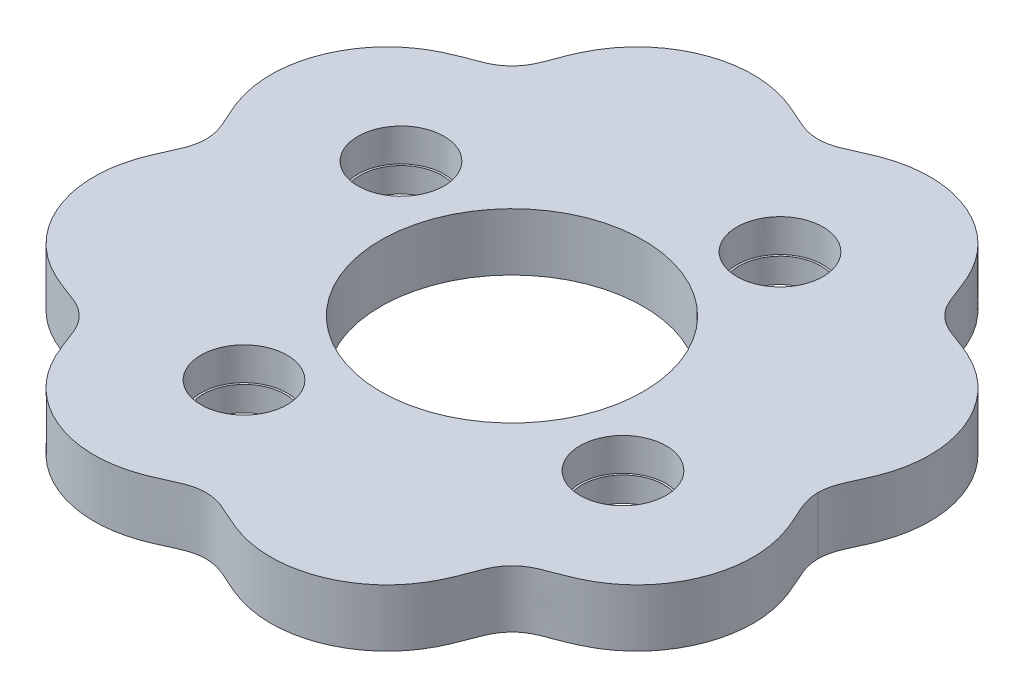
SolidWorks part; units mm, degrees
material "PET"
ref_plane "Front Plane" through (0, 0, 0) normal (0, 0, 1) x (1, 0, 0)
ref_plane "Top Plane" through (0, 0, 0) normal (0, 1, 0) x (1, 0, 0)
ref_plane "Right Plane" through (0, 0, 0) normal (1, 0, 0) x (0, 0, -1)
sketch "Sketch2" plane through (0, 0, 0) normal (0, 1, 0) x (1, 0, 0)
  line L0 (-37.5, 0) -> (37.5, 0) construction
  spline S0 degree 4 poles (36.9805, 20.0285) (37.2753, 19.6778) (37.8347, 18.9513) (38.4555, 17.9854) (39.0737, 16.7557) (39.5005, 15.6923) (39.7876, 14.8217) (40.0191, 13.9346) (40.1939, 13.0347) (40.3111, 12.1255) (40.3698, 11.2106) (40.3695, 10.2938) (40.3175, 9.4934) (40.2359, 8.8108) (40.1529, 8.3024) (40.0885, 7.9647) (40.0287, 7.6841) (39.9777, 7.4611) (39.9238, 7.2412) (39.8664, 7.0219) (39.8025, 6.7937) (39.7309, 6.5533) (39.6637, 6.3374) (39.6136, 6.1836) (39.5479, 5.991) (39.4755, 5.7851) (39.4027, 5.5855) (39.3311, 5.3965) (39.2407, 5.1663) (39.1279, 4.8896) (38.9903, 4.5651) (38.8283, 4.1989) (38.6621, 3.8341) (38.4352, 3.3438) (38.1502, 2.7272) (37.8212, 1.946) (37.5468, 0.9653) (37.4535, -0.0911) (37.5698, -1.0461) (37.7995, -1.8451) (38.0553, -2.5006) (38.2844, -3.0188) (38.5476, -3.5861) (38.8343, -4.2072) (39.213, -5.0714) (39.6429, -6.1955) (40.0348, -7.5456) (40.3091, -9.1291) (40.4025, -10.7334) (40.2923, -12.7392) (39.8007, -15.1154) (38.875, -17.3723) (37.5505, -19.4168) (36.2019, -20.9371) (34.9913, -22.0223) (33.6644, -22.9618) (32.4189, -23.6484) (31.3072, -24.1448) (30.4154, -24.4925) (29.7608, -24.7333) (29.1593, -24.9537) (28.6152, -25.1661) (27.9682, -25.4558) (27.2425, -25.8692) (26.4868, -26.4785) (25.7889, -27.3386) (25.3334, -28.1996) (25.0208, -28.9789) (24.7562, -29.6972) (24.5201, -30.3421) (24.1768, -31.23) (23.6857, -32.344) (23.006, -33.5933) (22.0744, -34.9257) (20.9963, -36.1426) (19.484, -37.5001) (17.4364, -38.8435) (15.1658, -39.787) (12.7656, -40.2907) (10.7279, -40.4037) (9.0981, -40.3067) (7.4903, -40.0231) (6.1205, -39.6185) (4.9809, -39.1759) (3.9811, -38.7332) (3.1077, -38.3232) (2.1628, -37.8962) (1.1027, -37.5687) (0, -37.4517) (-1.1027, -37.5687) (-2.1628, -37.8962) (-3.1077, -38.3232) (-3.9811, -38.7332) (-4.9809, -39.1759) (-6.1205, -39.6185) (-7.4903, -40.0231) (-9.0981, -40.3067) (-10.7279, -40.4037) (-12.7656, -40.2907) (-15.1658, -39.787) (-17.4364, -38.8435) (-19.484, -37.5001) (-20.9963, -36.1426) (-22.0744, -34.9257) (-23.006, -33.5933) (-23.6856, -32.3439) (-24.1768, -31.23) (-24.5707, -30.2109) (-24.8996, -29.3004) (-25.2674, -28.3245) (-25.7889, -27.3386) (-26.4868, -26.4785) (-27.2424, -25.8692) (-27.9682, -25.4558) (-28.6151, -25.166) (-29.1593, -24.9537) (-29.7608, -24.7333) (-30.4154, -24.4925) (-31.3072, -24.1448) (-32.4189, -23.6484) (-33.6644, -22.9618) (-34.9913, -22.0223) (-36.2019, -20.9371) (-37.5505, -19.4168) (-38.875, -17.3723) (-39.8007, -15.1154) (-40.2923, -12.7392) (-40.4025, -10.7334) (-40.3091, -9.1291) (-40.0348, -7.5456) (-39.6429, -6.1955) (-39.213, -5.0714) (-38.8343, -4.2072) (-38.5476, -3.5861) (-38.2844, -3.0188) (-38.0553, -2.5006) (-37.7995, -1.8451) (-37.5698, -1.0461) (-37.4535, -0.0911) (-37.5468, 0.9653) (-37.8212, 1.946) (-38.1502, 2.7272) (-38.4352, 3.3438) (-38.6621, 3.8341) (-38.8283, 4.1989) (-38.9903, 4.5651) (-39.1279, 4.8896) (-39.2407, 5.1663) (-39.3311, 5.3965) (-39.4027, 5.5855) (-39.4755, 5.7851) (-39.5479, 5.991) (-39.6136, 6.1836) (-39.6637, 6.3374) (-39.7309, 6.5533) (-39.8025, 6.7937) (-39.8664, 7.0219) (-39.9238, 7.2412) (-39.9777, 7.4611) (-40.0287, 7.6841) (-40.0885, 7.9647) (-40.1529, 8.3024) (-40.2359, 8.8108) (-40.3175, 9.4934) (-40.3695, 10.2938) (-40.3698, 11.2106) (-40.3111, 12.1255) (-40.1939, 13.0347) (-40.0191, 13.9346) (-39.7876, 14.8217) (-39.5005, 15.6923) (-39.0737, 16.7557) (-38.4555, 17.9854) (-37.8347, 18.9513) (-37.2753, 19.6778) (-36.9805, 20.0285) knots 0 0 0 0 0 0.010311 0.020621 0.025777 0.030932 0.036087 0.041243 0.046398 0.051553 0.056709 0.061864 0.067019 0.069597 0.072175 0.073463 0.074752 0.076041 0.07733 0.078618 0.079907 0.081196 0.082485 0.083613 0.084741 0.085869 0.086997 0.088125 0.089253 0.091509 0.093765 0.09602 0.098276 0.100532 0.105923 0.111314 0.117336 0.123359 0.129627 0.132815 0.136003 0.139191 0.142379 0.146891 0.151403 0.160427 0.169451 0.178475 0.1875 0.196524 0.214573 0.232831 0.24196 0.251089 0.260218 0.269348 0.278476 0.28304 0.287605 0.29089 0.294176 0.297462 0.300748 0.306838 0.312927 0.319161 0.325494 0.32866 0.331826 0.33639 0.340955 0.350083 0.359212 0.368341 0.37747 0.386599 0.404858 0.423193 0.432361 0.441528 0.450696 0.459863 0.46903 0.473614 0.478197 0.484473 0.490748 0.496943 0.503057 0.509252 0.515527 0.521803 0.526386 0.53097 0.540137 0.549304 0.558472 0.567639 0.576807 0.595142 0.613401 0.62253 0.631659 0.640788 0.649917 0.659045 0.66361 0.668174 0.674506 0.680839 0.687073 0.693162 0.699252 0.702538 0.705824 0.70911 0.712395 0.71696 0.721524 0.730652 0.739782 0.748911 0.75804 0.767169 0.785427 0.803476 0.8125 0.821525 0.830549 0.839573 0.848597 0.853109 0.857621 0.860809 0.863997 0.867185 0.870373 0.876641 0.882664 0.888686 0.894077 0.899468 0.901724 0.90398 0.906235 0.908491 0.910747 0.911875 0.913003 0.914131 0.915259 0.916387 0.917515 0.918804 0.920093 0.921382 0.92267 0.923959 0.925248 0.926537 0.927825 0.930403 0.932981 0.938136 0.943291 0.948447 0.953602 0.958757 0.963913 0.969068 0.974223 0.979379 0.989689 1 1 1 1 1 construction
  spline S1 degree 4 poles (37.5, 0) (37.5, -0.1537) (37.5167, -0.5857) (37.6013, -1.1559) (37.7995, -1.8451) (38.0553, -2.5006) (38.2844, -3.0188) (38.5476, -3.5861) (38.8343, -4.2072) (39.213, -5.0714) (39.6429, -6.1955) (40.0348, -7.5456) (40.3091, -9.1291) (40.4025, -10.7334) (40.2923, -12.7392) (39.8007, -15.1154) (38.875, -17.3723) (37.5505, -19.4168) (36.2019, -20.9371) (34.9913, -22.0223) (33.6644, -22.9618) (32.4189, -23.6484) (31.3072, -24.1448) (30.4154, -24.4925) (29.7608, -24.7333) (29.1593, -24.9537) (28.6152, -25.1661) (27.9682, -25.4558) (27.2425, -25.8692) (26.4868, -26.4785) (25.7889, -27.3386) (25.3334, -28.1996) (25.0208, -28.9789) (24.7562, -29.6972) (24.5201, -30.3421) (24.1768, -31.23) (23.6857, -32.344) (23.006, -33.5933) (22.0744, -34.9257) (20.9963, -36.1426) (19.484, -37.5001) (17.4364, -38.8435) (15.1658, -39.787) (12.7656, -40.2907) (10.7279, -40.4037) (9.0981, -40.3067) (7.4903, -40.0231) (6.1205, -39.6185) (4.9809, -39.1759) (3.9811, -38.7332) (3.1077, -38.3232) (2.1628, -37.8962) (1.1027, -37.5687) (0, -37.4517) (-1.1027, -37.5687) (-2.1628, -37.8962) (-3.1077, -38.3232) (-3.9811, -38.7332) (-4.9809, -39.1759) (-6.1205, -39.6185) (-7.4903, -40.0231) (-9.0981, -40.3067) (-10.7279, -40.4037) (-12.7656, -40.2907) (-15.1658, -39.787) (-17.4364, -38.8435) (-19.484, -37.5001) (-20.9963, -36.1426) (-22.0744, -34.9257) (-23.006, -33.5933) (-23.6856, -32.3439) (-24.1768, -31.23) (-24.5707, -30.2109) (-24.8996, -29.3004) (-25.2674, -28.3245) (-25.7889, -27.3386) (-26.4868, -26.4785) (-27.2424, -25.8692) (-27.9682, -25.4558) (-28.6151, -25.166) (-29.1593, -24.9537) (-29.7608, -24.7333) (-30.4154, -24.4925) (-31.3072, -24.1448) (-32.4189, -23.6484) (-33.6644, -22.9618) (-34.9913, -22.0223) (-36.2019, -20.9371) (-37.5505, -19.4168) (-38.875, -17.3723) (-39.8007, -15.1154) (-40.2923, -12.7392) (-40.4025, -10.7334) (-40.3091, -9.1291) (-40.0348, -7.5456) (-39.6429, -6.1955) (-39.213, -5.0714) (-38.8343, -4.2072) (-38.5476, -3.5861) (-38.2844, -3.0188) (-38.0553, -2.5006) (-37.7995, -1.8451) (-37.6013, -1.1559) (-37.5167, -0.5857) (-37.5, -0.1537) (-37.5, 0) knots 0.119901 0.119901 0.119901 0.119901 0.119901 0.123359 0.129627 0.132815 0.136003 0.139191 0.142379 0.146891 0.151403 0.160427 0.169451 0.178475 0.1875 0.196524 0.214573 0.232831 0.24196 0.251089 0.260218 0.269348 0.278476 0.28304 0.287605 0.29089 0.294176 0.297462 0.300748 0.306838 0.312927 0.319161 0.325494 0.32866 0.331826 0.33639 0.340955 0.350083 0.359212 0.368341 0.37747 0.386599 0.404858 0.423193 0.432361 0.441528 0.450696 0.459863 0.46903 0.473614 0.478197 0.484473 0.490748 0.496943 0.503057 0.509252 0.515527 0.521803 0.526386 0.53097 0.540137 0.549304 0.558472 0.567639 0.576807 0.595142 0.613401 0.62253 0.631659 0.640788 0.649917 0.659045 0.66361 0.668174 0.674506 0.680839 0.687073 0.693162 0.699252 0.702538 0.705824 0.70911 0.712395 0.71696 0.721524 0.730652 0.739782 0.748911 0.75804 0.767169 0.785427 0.803476 0.8125 0.821525 0.830549 0.839573 0.848597 0.853109 0.857621 0.860809 0.863997 0.867185 0.870373 0.876641 0.880099 0.880099 0.880099 0.880099 0.880099
  spline S2 degree 4 poles (37.5, 0) (37.5, 0.1537) (37.5167, 0.5857) (37.6013, 1.1559) (37.7995, 1.8451) (38.0553, 2.5006) (38.2844, 3.0188) (38.5476, 3.5861) (38.8343, 4.2072) (39.213, 5.0714) (39.6429, 6.1955) (40.0348, 7.5456) (40.3091, 9.1291) (40.4025, 10.7334) (40.2923, 12.7392) (39.8007, 15.1154) (38.875, 17.3723) (37.5505, 19.4168) (36.2019, 20.9371) (34.9913, 22.0223) (33.6644, 22.9618) (32.4189, 23.6484) (31.3072, 24.1448) (30.4154, 24.4925) (29.7608, 24.7333) (29.1593, 24.9537) (28.6152, 25.1661) (27.9682, 25.4558) (27.2425, 25.8692) (26.4868, 26.4785) (25.7889, 27.3386) (25.3334, 28.1996) (25.0208, 28.9789) (24.7562, 29.6972) (24.5201, 30.3421) (24.1768, 31.23) (23.6857, 32.344) (23.006, 33.5933) (22.0744, 34.9257) (20.9963, 36.1426) (19.484, 37.5001) (17.4364, 38.8435) (15.1658, 39.787) (12.7656, 40.2907) (10.7279, 40.4037) (9.0981, 40.3067) (7.4903, 40.0231) (6.1205, 39.6185) (4.9809, 39.1759) (3.9811, 38.7332) (3.1077, 38.3232) (2.1628, 37.8962) (1.1027, 37.5687) (0, 37.4517) (-1.1027, 37.5687) (-2.1628, 37.8962) (-3.1077, 38.3232) (-3.9811, 38.7332) (-4.9809, 39.1759) (-6.1205, 39.6185) (-7.4903, 40.0231) (-9.0981, 40.3067) (-10.7279, 40.4037) (-12.7656, 40.2907) (-15.1658, 39.787) (-17.4364, 38.8435) (-19.484, 37.5001) (-20.9963, 36.1426) (-22.0744, 34.9257) (-23.006, 33.5933) (-23.6856, 32.3439) (-24.1768, 31.23) (-24.5707, 30.2109) (-24.8996, 29.3004) (-25.2674, 28.3245) (-25.7889, 27.3386) (-26.4868, 26.4785) (-27.2424, 25.8692) (-27.9682, 25.4558) (-28.6151, 25.166) (-29.1593, 24.9537) (-29.7608, 24.7333) (-30.4154, 24.4925) (-31.3072, 24.1448) (-32.4189, 23.6484) (-33.6644, 22.9618) (-34.9913, 22.0223) (-36.2019, 20.9371) (-37.5505, 19.4168) (-38.875, 17.3723) (-39.8007, 15.1154) (-40.2923, 12.7392) (-40.4025, 10.7334) (-40.3091, 9.1291) (-40.0348, 7.5456) (-39.6429, 6.1955) (-39.213, 5.0714) (-38.8343, 4.2072) (-38.5476, 3.5861) (-38.2844, 3.0188) (-38.0553, 2.5006) (-37.7995, 1.8451) (-37.6013, 1.1559) (-37.5167, 0.5857) (-37.5, 0.1537) (-37.5, 0) knots 0.119901 0.119901 0.119901 0.119901 0.119901 0.123359 0.129627 0.132815 0.136003 0.139191 0.142379 0.146891 0.151403 0.160427 0.169451 0.178475 0.1875 0.196524 0.214573 0.232831 0.24196 0.251089 0.260218 0.269348 0.278476 0.28304 0.287605 0.29089 0.294176 0.297462 0.300748 0.306838 0.312927 0.319161 0.325494 0.32866 0.331826 0.33639 0.340955 0.350083 0.359212 0.368341 0.37747 0.386599 0.404858 0.423193 0.432361 0.441528 0.450696 0.459863 0.46903 0.473614 0.478197 0.484473 0.490748 0.496943 0.503057 0.509252 0.515527 0.521803 0.526386 0.53097 0.540137 0.549304 0.558472 0.567639 0.576807 0.595142 0.613401 0.62253 0.631659 0.640788 0.649917 0.659045 0.66361 0.668174 0.674506 0.680839 0.687073 0.693162 0.699252 0.702538 0.705824 0.70911 0.712395 0.71696 0.721524 0.730652 0.739782 0.748911 0.75804 0.767169 0.785427 0.803476 0.8125 0.821525 0.830549 0.839573 0.848597 0.853109 0.857621 0.860809 0.863997 0.867185 0.870373 0.876641 0.880099 0.880099 0.880099 0.880099 0.880099
extrude "Boss-Extrude1" add sketch "Sketch2" along normal blind 7 contours S2 S1
sketch "Sketch3" plane through (0, 7, 0) normal (0, 1, 0) x (1, 0, 0)
  line L0 (0, 0) -> (39.2649, -16.264) construction
  circle A0 centre (0, 0) radius 16
  circle A1 centre (23.097, -9.5671) radius 5.25
  circle A3 centre (-9.5671, -23.097) radius 5.25
  circle A4 centre (-23.097, 9.5671) radius 5.25
  circle A5 centre (9.5671, 23.097) radius 5.25
  spline S0 degree 4 poles (37.5, 0) (37.5, -0.1537) (37.5167, -0.5857) (37.6013, -1.1559) (37.7995, -1.8451) (38.0553, -2.5006) (38.2844, -3.0188) (38.5476, -3.5861) (38.8343, -4.2072) (39.213, -5.0714) (39.6429, -6.1955) (40.0348, -7.5456) (40.3091, -9.1291) (40.4025, -10.7334) (40.2923, -12.7392) (39.8007, -15.1154) (38.875, -17.3723) (37.5505, -19.4168) (36.2019, -20.9371) (34.9913, -22.0223) (33.6644, -22.9618) (32.4189, -23.6484) (31.3072, -24.1448) (30.4154, -24.4925) (29.7608, -24.7333) (29.1593, -24.9537) (28.6152, -25.1661) (27.9682, -25.4558) (27.2425, -25.8692) (26.4868, -26.4785) (25.7889, -27.3386) (25.3334, -28.1996) (25.0208, -28.9789) (24.7562, -29.6972) (24.5201, -30.3421) (24.1768, -31.23) (23.6857, -32.344) (23.006, -33.5933) (22.0744, -34.9257) (20.9963, -36.1426) (19.484, -37.5001) (17.4364, -38.8435) (15.1658, -39.787) (12.7656, -40.2907) (10.7279, -40.4037) (9.0981, -40.3067) (7.4903, -40.0231) (6.1205, -39.6185) (4.9809, -39.1759) (3.9811, -38.7332) (3.1077, -38.3232) (2.1628, -37.8962) (1.1027, -37.5687) (0, -37.4517) (-1.1027, -37.5687) (-2.1628, -37.8962) (-3.1077, -38.3232) (-3.9811, -38.7332) (-4.9809, -39.1759) (-6.1205, -39.6185) (-7.4903, -40.0231) (-9.0981, -40.3067) (-10.7279, -40.4037) (-12.7656, -40.2907) (-15.1658, -39.787) (-17.4364, -38.8435) (-19.484, -37.5001) (-20.9963, -36.1426) (-22.0744, -34.9257) (-23.006, -33.5933) (-23.6856, -32.3439) (-24.1768, -31.23) (-24.5707, -30.2109) (-24.8996, -29.3004) (-25.2674, -28.3245) (-25.7889, -27.3386) (-26.4868, -26.4785) (-27.2424, -25.8692) (-27.9682, -25.4558) (-28.6151, -25.166) (-29.1593, -24.9537) (-29.7608, -24.7333) (-30.4154, -24.4925) (-31.3072, -24.1448) (-32.4189, -23.6484) (-33.6644, -22.9618) (-34.9913, -22.0223) (-36.2019, -20.9371) (-37.5505, -19.4168) (-38.875, -17.3723) (-39.8007, -15.1154) (-40.2923, -12.7392) (-40.4025, -10.7334) (-40.3091, -9.1291) (-40.0348, -7.5456) (-39.6429, -6.1955) (-39.213, -5.0714) (-38.8343, -4.2072) (-38.5476, -3.5861) (-38.2844, -3.0188) (-38.0553, -2.5006) (-37.7995, -1.8451) (-37.6013, -1.1559) (-37.5167, -0.5857) (-37.5, -0.1537) (-37.5, 0) knots 0.119901 0.119901 0.119901 0.119901 0.119901 0.123359 0.129627 0.132815 0.136003 0.139191 0.142379 0.146891 0.151403 0.160427 0.169451 0.178475 0.1875 0.196524 0.214573 0.232831 0.24196 0.251089 0.260218 0.269348 0.278476 0.28304 0.287605 0.29089 0.294176 0.297462 0.300748 0.306838 0.312927 0.319161 0.325494 0.32866 0.331826 0.33639 0.340955 0.350083 0.359212 0.368341 0.37747 0.386599 0.404858 0.423193 0.432361 0.441528 0.450696 0.459863 0.46903 0.473614 0.478197 0.484473 0.490748 0.496943 0.503057 0.509252 0.515527 0.521803 0.526386 0.53097 0.540137 0.549304 0.558472 0.567639 0.576807 0.595142 0.613401 0.62253 0.631659 0.640788 0.649917 0.659045 0.66361 0.668174 0.674506 0.680839 0.687073 0.693162 0.699252 0.702538 0.705824 0.70911 0.712395 0.71696 0.721524 0.730652 0.739782 0.748911 0.75804 0.767169 0.785427 0.803476 0.8125 0.821525 0.830549 0.839573 0.848597 0.853109 0.857621 0.860809 0.863997 0.867185 0.870373 0.876641 0.880099 0.880099 0.880099 0.880099 0.880099 construction
  point P18 (0, 0)
  dimension "D1" = 32
  dimension "D2" = 10.5
  dimension "D4" = 25
  dimension "D5" = 4
extrude "Cut-Extrude1" cut sketch "Sketch3" against normal blind 7
sketch "Sketch4" plane through (0, 0, 0) normal (0, -1, 0) x (1, 0, 0)
  spline S4 degree 3 poles (-3922.8422, 946.158) (-178.574, 87.803) (-28.4361, 25.2826) (-37.8533, -2.585) (-38.1471, -3.1952) (-38.7107, -4.4187) (-38.9828, -5.0336) (-39.4508, -6.2882) (-39.648, -6.9276) (-39.8757, -7.9088) (-39.9403, -8.2396) (-40.0461, -8.9088) (-40.0873, -9.2487) (-40.1729, -10.2702) (-40.1796, -10.9476) (-40.0964, -12.2955) (-40.0066, -12.966) (-39.7983, -13.9664) (-39.7162, -14.2999) (-39.5299, -14.9551) (-39.4254, -15.2779) (-39.079, -16.2318) (-38.8042, -16.8488) (-38.1662, -18.0446) (-37.7995, -18.6276) (-36.9951, -19.7223) (-36.557, -20.2365) (-35.6094, -21.1989) (-35.0988, -21.6477) (-34.0068, -22.4733) (-33.4366, -22.8413) (-32.2526, -23.4966) (-31.6381, -23.7828) (-30.6936, -24.1698) (-30.3749, -24.292) (-29.7353, -24.5302) (-29.4141, -24.6459) (-28.7761, -24.8878) (-28.4596, -25.0146) (-27.8419, -25.305) (-27.5385, -25.4704) (-26.9685, -25.8482) (-26.7027, -26.0593) (-26.2122, -26.5296) (-25.9857, -26.7918) (-25.5865, -27.3477) (-25.4133, -27.6409) (-25.1061, -28.2501) (-24.9721, -28.5662) (-24.722, -29.2071) (-24.6047, -29.5314) (-24.366, -30.178) (-24.2449, -30.5004) (-23.862, -31.4579) (-23.58, -32.0828) (-22.9307, -33.2897) (-22.5646, -33.8723) (-21.9447, -34.7109) (-21.7254, -34.9856) (-21.2703, -35.5135) (-21.0341, -35.7676) (-20.2998, -36.5011) (-19.7765, -36.9518) (-18.6627, -37.777) (-18.0672, -38.1536) (-16.8421, -38.8083) (-16.2104, -39.0887) (-15.2346, -39.4401) (-14.9046, -39.5456) (-14.235, -39.7331) (-13.894, -39.8152) (-12.1831, -40.161) (-10.8043, -40.2342) (-9.068, -40.0667) (-8.72, -40.0198) (-8.034, -39.9014) (-7.6946, -39.8297) (-6.6868, -39.5791) (-6.0289, -39.3634) (-4.7349, -38.8569) (-4.0997, -38.5639) (-2.8312, -37.9786) (-2.1955, -37.6898) (-1.1773, -37.4157) (-0.8309, -37.3518) (-0.1388, -37.2909) (0.2091, -37.2929) (0.9087, -37.3638) (1.2541, -37.4328) (1.9235, -37.621) (2.2502, -37.7405) (2.8946, -38.0077) (3.2126, -38.1544) (3.8487, -38.4482) (4.1667, -38.5954) (5.126, -39.018) (5.773, -39.274) (7.0935, -39.6938) (7.7666, -39.859) (8.7979, -40.0311) (9.1453, -40.076) (9.8476, -40.1396) (10.2044, -40.1583) (11.9811, -40.1834) (13.3741, -39.9912) (15.0807, -39.4906) (15.419, -39.3775) (16.0811, -39.1284) (16.4062, -38.9921) (17.364, -38.5485) (17.9792, -38.2067) (18.8662, -37.6232) (19.1571, -37.416) (19.72, -36.9818) (19.9916, -36.7554) (20.7778, -36.0486) (21.2637, -35.5408) (21.9348, -34.7238) (22.1489, -34.4422) (22.5573, -33.8603) (22.7513, -33.5603) (23.2966, -32.6452) (23.6131, -32.0104) (24.035, -31.0305) (24.1671, -30.6994) (24.4207, -30.0336) (24.5422, -29.6985) (24.7899, -29.0303) (24.9163, -28.6973) (25.203, -28.0449) (25.3653, -27.7235) (25.7389, -27.1186) (25.9496, -26.8348) (26.4253, -26.3096) (26.6934, -26.0663) (27.2624, -25.6405) (27.5646, -25.4559) (28.1962, -25.1299) (28.5258, -24.9886) (29.1951, -24.726) (29.5346, -24.6036) (30.211, -24.3537) (30.5481, -24.2267) (31.5472, -23.8241) (32.1968, -23.526) (33.4451, -22.8381) (34.0446, -22.4496) (34.9029, -21.793) (35.1822, -21.5619) (35.7264, -21.0739) (35.9929, -20.8154) (36.7549, -20.0151) (37.2156, -19.4476) (38.0459, -18.2477) (38.4158, -17.6149) (39.0608, -16.2832) (39.3278, -15.6011) (39.7553, -14.2058) (39.9157, -13.4925) (40.0733, -12.3983) (40.1117, -12.0294) (40.1591, -11.2964) (40.1684, -10.9307) (40.1534, -9.836) (40.0865, -9.1093) (39.8999, -8.0241) (39.8229, -7.6619) (39.642, -6.9461) (39.5382, -6.593) (39.1911, -5.5467) (38.9098, -4.8672) (38.4549, -3.8599) (38.2979, -3.5261) (37.9924, -2.8554) (37.8446, -2.5182) (37.5906, -1.8289) (37.4849, -1.4765) (32.1786, 25.0386) (201.3355, 100.2032) (2476.1492, -3163.1826) knots -0.660189 -0.660189 -0.660189 -0.660189 0.015625 0.015625 0.03125 0.03125 0.046875 0.046875 0.0625 0.0625 0.070312 0.070312 0.078125 0.078125 0.09375 0.09375 0.109375 0.109375 0.117187 0.117187 0.125 0.125 0.140625 0.140625 0.15625 0.15625 0.171875 0.171875 0.1875 0.1875 0.203125 0.203125 0.21875 0.21875 0.226562 0.226562 0.234375 0.234375 0.242187 0.242187 0.25 0.25 0.257812 0.257812 0.265625 0.265625 0.273437 0.273437 0.28125 0.28125 0.289062 0.289062 0.296875 0.296875 0.3125 0.3125 0.328125 0.328125 0.335937 0.335937 0.34375 0.34375 0.359375 0.359375 0.375 0.375 0.390625 0.390625 0.398437 0.398437 0.40625 0.40625 0.4375 0.4375 0.445312 0.445312 0.453125 0.453125 0.46875 0.46875 0.484375 0.484375 0.5 0.5 0.507812 0.507812 0.515625 0.515625 0.523437 0.523437 0.53125 0.53125 0.539062 0.539062 0.546875 0.546875 0.5625 0.5625 0.578125 0.578125 0.585937 0.585937 0.59375 0.59375 0.625 0.625 0.632812 0.632812 0.640625 0.640625 0.65625 0.65625 0.664062 0.664062 0.671875 0.671875 0.6875 0.6875 0.695312 0.695312 0.703125 0.703125 0.71875 0.71875 0.726562 0.726562 0.734375 0.734375 0.742187 0.742187 0.75 0.75 0.757812 0.757812 0.765625 0.765625 0.773437 0.773437 0.78125 0.78125 0.789062 0.789062 0.796875 0.796875 0.8125 0.8125 0.828125 0.828125 0.835937 0.835937 0.84375 0.84375 0.859375 0.859375 0.875 0.875 0.890625 0.890625 0.90625 0.90625 0.914062 0.914062 0.921875 0.921875 0.9375 0.9375 0.945312 0.945312 0.953125 0.953125 0.96875 0.96875 0.976562 0.976562 0.984375 0.984375 0.992187 0.992187 1.553035 1.553035 1.553035 1.553035 only from (-37.3, 0) to (37.3, 0)
  spline S5 degree 3 poles (3937.7854, -882.9619) (188.4371, -88.2123) (28.4038, -25.8804) (37.8317, 2.5321) (38.1169, 3.1309) (38.67, 4.3291) (38.9391, 4.9306) (39.406, 6.1564) (39.605, 6.7803) (39.9166, 8.056) (40.0298, 8.7075) (40.1293, 9.7073) (40.1505, 10.0435) (40.1686, 10.7108) (40.1657, 11.0433) (40.1219, 12.0378) (40.046, 12.6965) (39.8009, 14.0056) (39.6299, 14.66) (39.2033, 15.9228) (38.9476, 16.535) (38.3524, 17.7213) (38.0116, 18.2974) (36.8656, 19.953) (35.9651, 20.9257) (34.6682, 21.9774) (34.3991, 22.18) (33.8491, 22.5642) (33.5682, 22.7458) (32.7084, 23.2605) (32.1122, 23.5629) (30.8834, 24.1035) (30.2535, 24.3387) (28.9923, 24.8027) (28.3593, 25.0337) (27.173, 25.6725) (26.6404, 26.0718) (25.7322, 27.0751) (25.3881, 27.6463) (24.9705, 28.5655) (24.8471, 28.881) (24.6087, 29.5163) (24.4932, 29.836) (24.1362, 30.7892) (23.8828, 31.4162) (23.0112, 33.2354) (22.2825, 34.3665) (21.1418, 35.6532) (20.9009, 35.9055) (20.4029, 36.3896) (20.1462, 36.621) (19.3542, 37.2845) (18.7968, 37.6859) (17.9172, 38.2274) (17.6167, 38.3978) (17.0008, 38.7178) (16.6853, 38.8674) (15.7319, 39.2776) (15.0821, 39.5029) (13.7545, 39.8588) (13.0763, 39.9895) (11.6925, 40.1507) (11.0033, 40.1794) (9.6304, 40.1362) (8.9466, 40.0641) (7.9251, 39.8793) (7.5841, 39.8046) (6.9111, 39.6316) (6.5788, 39.5334) (5.5932, 39.2068) (4.9518, 38.945) (4.0012, 38.5197) (3.6862, 38.3727) (3.0549, 38.0823) (2.7387, 37.939) (1.7744, 37.5551) (1.1084, 37.3657) (-0.3132, 37.2631) (-1.0098, 37.3537) (-2.3731, 37.7595) (-3.0204, 38.0657) (-4.3192, 38.6656) (-4.971, 38.9584) (-6.3033, 39.4574) (-6.9832, 39.6657) (-8.0287, 39.9006) (-8.3815, 39.9661) (-9.096, 40.0703) (-9.4592, 40.109) (-10.5423, 40.1818) (-11.2606, 40.1739) (-12.6902, 40.0495) (-13.4023, 39.9326) (-14.8151, 39.5876) (-15.4996, 39.3636) (-16.8266, 38.8168) (-17.469, 38.4941) (-18.4002, 37.9335) (-18.7053, 37.7335) (-19.294, 37.3147) (-19.5789, 37.095) (-20.4061, 36.4056) (-20.9207, 35.9057) (-21.636, 35.094) (-21.8657, 34.8121) (-22.3022, 34.2315) (-22.5079, 33.9343) (-23.0891, 33.0233) (-23.428, 32.3894) (-24.0267, 31.0784) (-24.2847, 30.4) (-24.7858, 29.0385) (-25.0297, 28.3549) (-25.5555, 27.397) (-25.7572, 27.0906) (-26.2108, 26.5294) (-26.4639, 26.2717) (-27.0247, 25.8042) (-27.3276, 25.5991) (-27.9582, 25.243) (-28.288, 25.0905) (-28.9629, 24.8128) (-29.3068, 24.687) (-29.9941, 24.4342) (-30.3374, 24.3073) (-31.3574, 23.9062) (-32.0234, 23.6106) (-33.3074, 22.9225) (-33.9261, 22.5314) (-34.8143, 21.8642) (-35.1027, 21.6291) (-35.6549, 21.1411) (-35.9202, 20.8872) (-36.6842, 20.0966) (-37.1512, 19.5312) (-37.7877, 18.6247) (-37.9897, 18.3116) (-38.3661, 17.6752) (-38.5409, 17.3513) (-39.0264, 16.3632) (-39.2984, 15.6825) (-39.7376, 14.2767) (-39.9046, 13.5479) (-40.12, 12.094) (-40.1708, 11.3634) (-40.1608, 10.2619) (-40.143, 9.8938) (-40.0776, 9.1558) (-40.03, 8.7868) (-39.8455, 7.6961) (-39.6659, 6.9845) (-39.2071, 5.5888) (-38.9258, 4.9045) (-38.4691, 3.8906) (-38.3112, 3.5547) (-38.0034, 2.8801) (-37.8539, 2.541) (-37.5965, 1.8472) (-37.4888, 1.4922) (-32.3669, -23.8258) (-185.1413, -99.6898) (-2326.352, 3274.32) knots -0.686781 -0.686781 -0.686781 -0.686781 0.015625 0.015625 0.03125 0.03125 0.046875 0.046875 0.0625 0.0625 0.078125 0.078125 0.085938 0.085938 0.09375 0.09375 0.109375 0.109375 0.125 0.125 0.140625 0.140625 0.15625 0.15625 0.1875 0.1875 0.195313 0.195313 0.203125 0.203125 0.21875 0.21875 0.234375 0.234375 0.25 0.25 0.265625 0.265625 0.28125 0.28125 0.289063 0.289063 0.296875 0.296875 0.3125 0.3125 0.34375 0.34375 0.351563 0.351563 0.359375 0.359375 0.375 0.375 0.382813 0.382813 0.390625 0.390625 0.40625 0.40625 0.421875 0.421875 0.4375 0.4375 0.453125 0.453125 0.460938 0.460938 0.46875 0.46875 0.484375 0.484375 0.492188 0.492188 0.5 0.5 0.515625 0.515625 0.53125 0.53125 0.546875 0.546875 0.5625 0.5625 0.578125 0.578125 0.585938 0.585938 0.59375 0.59375 0.609375 0.609375 0.625 0.625 0.640625 0.640625 0.65625 0.65625 0.664063 0.664063 0.671875 0.671875 0.6875 0.6875 0.695313 0.695313 0.703125 0.703125 0.71875 0.71875 0.734375 0.734375 0.75 0.75 0.757813 0.757813 0.765625 0.765625 0.773438 0.773438 0.78125 0.78125 0.789063 0.789063 0.796875 0.796875 0.8125 0.8125 0.828125 0.828125 0.835938 0.835938 0.84375 0.84375 0.859375 0.859375 0.867188 0.867188 0.875 0.875 0.890625 0.890625 0.90625 0.90625 0.921875 0.921875 0.929688 0.929688 0.9375 0.9375 0.953125 0.953125 0.96875 0.96875 0.976563 0.976563 0.984375 0.984375 0.992188 0.992188 1.522491 1.522491 1.522491 1.522491 only from (37.3, 0) to (-37.3, 0)
  spline S6 degree 3 poles (-37.3, 0) (-37.3, -0.6769) (-37.4276, -1.3255) (-37.8533, -2.585) (-38.1471, -3.1952) (-38.7107, -4.4187) (-38.9828, -5.0336) (-39.4508, -6.2882) (-39.648, -6.9276) (-39.8757, -7.9088) (-39.9403, -8.2396) (-40.0461, -8.9088) (-40.0873, -9.2487) (-40.1729, -10.2702) (-40.1796, -10.9476) (-40.0964, -12.2955) (-40.0066, -12.966) (-39.7983, -13.9664) (-39.7162, -14.2999) (-39.5299, -14.9551) (-39.4254, -15.2779) (-39.079, -16.2318) (-38.8042, -16.8488) (-38.1662, -18.0446) (-37.7995, -18.6276) (-36.9951, -19.7223) (-36.557, -20.2365) (-35.6094, -21.1989) (-35.0988, -21.6477) (-34.0068, -22.4733) (-33.4366, -22.8413) (-32.2526, -23.4966) (-31.6381, -23.7828) (-30.6936, -24.1698) (-30.3749, -24.292) (-29.7353, -24.5302) (-29.4141, -24.6459) (-28.7761, -24.8878) (-28.4596, -25.0146) (-27.8419, -25.305) (-27.5385, -25.4704) (-26.9685, -25.8482) (-26.7027, -26.0593) (-26.2122, -26.5296) (-25.9857, -26.7918) (-25.5865, -27.3477) (-25.4133, -27.6409) (-25.1061, -28.2501) (-24.9721, -28.5662) (-24.722, -29.2071) (-24.6047, -29.5314) (-24.366, -30.178) (-24.2449, -30.5004) (-23.862, -31.4579) (-23.58, -32.0828) (-22.9307, -33.2897) (-22.5646, -33.8723) (-21.9447, -34.7109) (-21.7254, -34.9856) (-21.2703, -35.5135) (-21.0341, -35.7676) (-20.2998, -36.5011) (-19.7765, -36.9518) (-18.6627, -37.777) (-18.0672, -38.1536) (-16.8421, -38.8083) (-16.2104, -39.0887) (-15.2346, -39.4401) (-14.9046, -39.5456) (-14.235, -39.7331) (-13.894, -39.8152) (-12.1831, -40.161) (-10.8043, -40.2342) (-9.068, -40.0667) (-8.72, -40.0198) (-8.034, -39.9014) (-7.6946, -39.8297) (-6.6868, -39.5791) (-6.0289, -39.3634) (-4.7349, -38.8569) (-4.0997, -38.5639) (-2.8312, -37.9786) (-2.1955, -37.6898) (-1.1773, -37.4157) (-0.8309, -37.3518) (-0.1388, -37.2909) (0.2091, -37.2929) (0.9087, -37.3638) (1.2541, -37.4328) (1.9235, -37.621) (2.2502, -37.7405) (2.8946, -38.0077) (3.2126, -38.1544) (3.8487, -38.4482) (4.1667, -38.5954) (5.126, -39.018) (5.773, -39.274) (7.0935, -39.6938) (7.7666, -39.859) (8.7979, -40.0311) (9.1453, -40.076) (9.8476, -40.1396) (10.2044, -40.1583) (11.9811, -40.1834) (13.3741, -39.9912) (15.0807, -39.4906) (15.419, -39.3775) (16.0811, -39.1284) (16.4062, -38.9921) (17.364, -38.5485) (17.9792, -38.2067) (18.8662, -37.6232) (19.1571, -37.416) (19.72, -36.9818) (19.9916, -36.7554) (20.7778, -36.0486) (21.2637, -35.5408) (21.9348, -34.7238) (22.1489, -34.4422) (22.5573, -33.8603) (22.7513, -33.5603) (23.2966, -32.6452) (23.6131, -32.0104) (24.035, -31.0305) (24.1671, -30.6994) (24.4207, -30.0336) (24.5422, -29.6985) (24.7899, -29.0303) (24.9163, -28.6973) (25.203, -28.0449) (25.3653, -27.7235) (25.7389, -27.1186) (25.9496, -26.8348) (26.4253, -26.3096) (26.6934, -26.0663) (27.2624, -25.6405) (27.5646, -25.4559) (28.1962, -25.1299) (28.5258, -24.9886) (29.1951, -24.726) (29.5346, -24.6036) (30.211, -24.3537) (30.5481, -24.2267) (31.5472, -23.8241) (32.1968, -23.526) (33.4451, -22.8381) (34.0446, -22.4496) (34.9029, -21.793) (35.1822, -21.5619) (35.7264, -21.0739) (35.9929, -20.8154) (36.7549, -20.0151) (37.2156, -19.4476) (38.0459, -18.2477) (38.4158, -17.6149) (39.0608, -16.2832) (39.3278, -15.6011) (39.7553, -14.2058) (39.9157, -13.4925) (40.0733, -12.3983) (40.1117, -12.0294) (40.1591, -11.2964) (40.1684, -10.9307) (40.1534, -9.836) (40.0865, -9.1093) (39.8999, -8.0241) (39.8229, -7.6619) (39.642, -6.9461) (39.5382, -6.593) (39.1911, -5.5467) (38.9098, -4.8672) (38.4549, -3.8599) (38.2979, -3.5261) (37.9924, -2.8554) (37.8446, -2.5182) (37.5906, -1.8289) (37.4849, -1.4765) (37.3391, -0.7479) (37.3, -0.3741) (37.3, 0) knots 0 0 0 0 0.015625 0.015625 0.03125 0.03125 0.046875 0.046875 0.0625 0.0625 0.070312 0.070312 0.078125 0.078125 0.09375 0.09375 0.109375 0.109375 0.117187 0.117187 0.125 0.125 0.140625 0.140625 0.15625 0.15625 0.171875 0.171875 0.1875 0.1875 0.203125 0.203125 0.21875 0.21875 0.226562 0.226562 0.234375 0.234375 0.242187 0.242187 0.25 0.25 0.257812 0.257812 0.265625 0.265625 0.273437 0.273437 0.28125 0.28125 0.289062 0.289062 0.296875 0.296875 0.3125 0.3125 0.328125 0.328125 0.335937 0.335937 0.34375 0.34375 0.359375 0.359375 0.375 0.375 0.390625 0.390625 0.398437 0.398437 0.40625 0.40625 0.4375 0.4375 0.445312 0.445312 0.453125 0.453125 0.46875 0.46875 0.484375 0.484375 0.5 0.5 0.507812 0.507812 0.515625 0.515625 0.523437 0.523437 0.53125 0.53125 0.539062 0.539062 0.546875 0.546875 0.5625 0.5625 0.578125 0.578125 0.585937 0.585937 0.59375 0.59375 0.625 0.625 0.632812 0.632812 0.640625 0.640625 0.65625 0.65625 0.664062 0.664062 0.671875 0.671875 0.6875 0.6875 0.695312 0.695312 0.703125 0.703125 0.71875 0.71875 0.726562 0.726562 0.734375 0.734375 0.742187 0.742187 0.75 0.75 0.757812 0.757812 0.765625 0.765625 0.773437 0.773437 0.78125 0.78125 0.789062 0.789062 0.796875 0.796875 0.8125 0.8125 0.828125 0.828125 0.835937 0.835937 0.84375 0.84375 0.859375 0.859375 0.875 0.875 0.890625 0.890625 0.90625 0.90625 0.914062 0.914062 0.921875 0.921875 0.9375 0.9375 0.945312 0.945312 0.953125 0.953125 0.96875 0.96875 0.976562 0.976562 0.984375 0.984375 0.992187 0.992187 1 1 1 1
  spline S7 degree 3 poles (37.3, 0) (37.3, 0.6601) (37.4214, 1.2955) (37.8317, 2.5321) (38.1169, 3.1309) (38.67, 4.3291) (38.9391, 4.9306) (39.406, 6.1564) (39.605, 6.7803) (39.9166, 8.056) (40.0298, 8.7075) (40.1293, 9.7073) (40.1505, 10.0435) (40.1686, 10.7108) (40.1657, 11.0433) (40.1219, 12.0378) (40.046, 12.6965) (39.8009, 14.0056) (39.6299, 14.66) (39.2033, 15.9228) (38.9476, 16.535) (38.3524, 17.7213) (38.0116, 18.2974) (36.8656, 19.953) (35.9651, 20.9257) (34.6682, 21.9774) (34.3991, 22.18) (33.8491, 22.5642) (33.5682, 22.7458) (32.7084, 23.2605) (32.1122, 23.5629) (30.8834, 24.1035) (30.2535, 24.3387) (28.9923, 24.8027) (28.3593, 25.0337) (27.173, 25.6725) (26.6404, 26.0718) (25.7322, 27.0751) (25.3881, 27.6463) (24.9705, 28.5655) (24.8471, 28.881) (24.6087, 29.5163) (24.4932, 29.836) (24.1362, 30.7892) (23.8828, 31.4162) (23.0112, 33.2354) (22.2825, 34.3665) (21.1418, 35.6532) (20.9009, 35.9055) (20.4029, 36.3896) (20.1462, 36.621) (19.3542, 37.2845) (18.7968, 37.6859) (17.9172, 38.2274) (17.6167, 38.3978) (17.0008, 38.7178) (16.6853, 38.8674) (15.7319, 39.2776) (15.0821, 39.5029) (13.7545, 39.8588) (13.0763, 39.9895) (11.6925, 40.1507) (11.0033, 40.1794) (9.6304, 40.1362) (8.9466, 40.0641) (7.9251, 39.8793) (7.5841, 39.8046) (6.9111, 39.6316) (6.5788, 39.5334) (5.5932, 39.2068) (4.9518, 38.945) (4.0012, 38.5197) (3.6862, 38.3727) (3.0549, 38.0823) (2.7387, 37.939) (1.7744, 37.5551) (1.1084, 37.3657) (-0.3132, 37.2631) (-1.0098, 37.3537) (-2.3731, 37.7595) (-3.0204, 38.0657) (-4.3192, 38.6656) (-4.971, 38.9584) (-6.3033, 39.4574) (-6.9832, 39.6657) (-8.0287, 39.9006) (-8.3815, 39.9661) (-9.096, 40.0703) (-9.4592, 40.109) (-10.5423, 40.1818) (-11.2606, 40.1739) (-12.6902, 40.0495) (-13.4023, 39.9326) (-14.8151, 39.5876) (-15.4996, 39.3636) (-16.8266, 38.8168) (-17.469, 38.4941) (-18.4002, 37.9335) (-18.7053, 37.7335) (-19.294, 37.3147) (-19.5789, 37.095) (-20.4061, 36.4056) (-20.9207, 35.9057) (-21.636, 35.094) (-21.8657, 34.8121) (-22.3022, 34.2315) (-22.5079, 33.9343) (-23.0891, 33.0233) (-23.428, 32.3894) (-24.0267, 31.0784) (-24.2847, 30.4) (-24.7858, 29.0385) (-25.0297, 28.3549) (-25.5555, 27.397) (-25.7572, 27.0906) (-26.2108, 26.5294) (-26.4639, 26.2717) (-27.0247, 25.8042) (-27.3276, 25.5991) (-27.9582, 25.243) (-28.288, 25.0905) (-28.9629, 24.8128) (-29.3068, 24.687) (-29.9941, 24.4342) (-30.3374, 24.3073) (-31.3574, 23.9062) (-32.0234, 23.6106) (-33.3074, 22.9225) (-33.9261, 22.5314) (-34.8143, 21.8642) (-35.1027, 21.6291) (-35.6549, 21.1411) (-35.9202, 20.8872) (-36.6842, 20.0966) (-37.1512, 19.5312) (-37.7877, 18.6247) (-37.9897, 18.3116) (-38.3661, 17.6752) (-38.5409, 17.3513) (-39.0264, 16.3632) (-39.2984, 15.6825) (-39.7376, 14.2767) (-39.9046, 13.5479) (-40.12, 12.094) (-40.1708, 11.3634) (-40.1608, 10.2619) (-40.143, 9.8938) (-40.0776, 9.1558) (-40.03, 8.7868) (-39.8455, 7.6961) (-39.6659, 6.9845) (-39.2071, 5.5888) (-38.9258, 4.9045) (-38.4691, 3.8906) (-38.3112, 3.5547) (-38.0034, 2.8801) (-37.8539, 2.541) (-37.5965, 1.8472) (-37.4888, 1.4922) (-37.3401, 0.7571) (-37.3, 0.3785) (-37.3, 0) knots 0 0 0 0 0.015625 0.015625 0.03125 0.03125 0.046875 0.046875 0.0625 0.0625 0.078125 0.078125 0.085938 0.085938 0.09375 0.09375 0.109375 0.109375 0.125 0.125 0.140625 0.140625 0.15625 0.15625 0.1875 0.1875 0.195313 0.195313 0.203125 0.203125 0.21875 0.21875 0.234375 0.234375 0.25 0.25 0.265625 0.265625 0.28125 0.28125 0.289063 0.289063 0.296875 0.296875 0.3125 0.3125 0.34375 0.34375 0.351563 0.351563 0.359375 0.359375 0.375 0.375 0.382813 0.382813 0.390625 0.390625 0.40625 0.40625 0.421875 0.421875 0.4375 0.4375 0.453125 0.453125 0.460938 0.460938 0.46875 0.46875 0.484375 0.484375 0.492188 0.492188 0.5 0.5 0.515625 0.515625 0.53125 0.53125 0.546875 0.546875 0.5625 0.5625 0.578125 0.578125 0.585938 0.585938 0.59375 0.59375 0.609375 0.609375 0.625 0.625 0.640625 0.640625 0.65625 0.65625 0.664063 0.664063 0.671875 0.671875 0.6875 0.6875 0.695313 0.695313 0.703125 0.703125 0.71875 0.71875 0.734375 0.734375 0.75 0.75 0.757813 0.757813 0.765625 0.765625 0.773438 0.773438 0.78125 0.78125 0.789063 0.789063 0.796875 0.796875 0.8125 0.8125 0.828125 0.828125 0.835938 0.835938 0.84375 0.84375 0.859375 0.859375 0.867188 0.867188 0.875 0.875 0.890625 0.890625 0.90625 0.90625 0.921875 0.921875 0.929688 0.929688 0.9375 0.9375 0.953125 0.953125 0.96875 0.96875 0.976563 0.976563 0.984375 0.984375 0.992188 0.992188 1 1 1 1
  spline S9 degree 4 poles (-3919.2032, 578.7026) (176.1956, 57.3236) (57.6018, -24.9049) (34.8011, -8.5868) (37.7995, 1.8451) (38.0553, 2.5006) (38.2844, 3.0188) (38.5476, 3.5861) (38.8343, 4.2072) (39.213, 5.0714) (39.6429, 6.1955) (40.0348, 7.5456) (40.3091, 9.1291) (40.4025, 10.7334) (40.2923, 12.7392) (39.8007, 15.1154) (38.875, 17.3723) (37.5505, 19.4168) (36.2019, 20.9371) (34.9913, 22.0223) (33.6644, 22.9618) (32.4189, 23.6484) (31.3072, 24.1448) (30.4154, 24.4925) (29.7608, 24.7333) (29.1593, 24.9537) (28.6152, 25.1661) (27.9682, 25.4558) (27.2425, 25.8692) (26.4868, 26.4785) (25.7889, 27.3386) (25.3334, 28.1996) (25.0208, 28.9789) (24.7562, 29.6972) (24.5201, 30.3421) (24.1768, 31.23) (23.6857, 32.344) (23.006, 33.5933) (22.0744, 34.9257) (20.9963, 36.1426) (19.484, 37.5001) (17.4364, 38.8435) (15.1658, 39.787) (12.7656, 40.2907) (10.7279, 40.4037) (9.0981, 40.3067) (7.4903, 40.0231) (6.1205, 39.6185) (4.9809, 39.1759) (3.9811, 38.7332) (3.1077, 38.3232) (2.1628, 37.8962) (1.1027, 37.5687) (0, 37.4517) (-1.1027, 37.5687) (-2.1628, 37.8962) (-3.1077, 38.3232) (-3.9811, 38.7332) (-4.9809, 39.1759) (-6.1205, 39.6185) (-7.4903, 40.0231) (-9.0981, 40.3067) (-10.7279, 40.4037) (-12.7656, 40.2907) (-15.1658, 39.787) (-17.4364, 38.8435) (-19.484, 37.5001) (-20.9963, 36.1426) (-22.0744, 34.9257) (-23.006, 33.5933) (-23.6856, 32.3439) (-24.1768, 31.23) (-24.5707, 30.2109) (-24.8996, 29.3004) (-25.2674, 28.3245) (-25.7889, 27.3386) (-26.4868, 26.4785) (-27.2424, 25.8692) (-27.9682, 25.4558) (-28.6151, 25.166) (-29.1593, 24.9537) (-29.7608, 24.7333) (-30.4154, 24.4925) (-31.3072, 24.1448) (-32.4189, 23.6484) (-33.6644, 22.9618) (-34.9913, 22.0223) (-36.2019, 20.9371) (-37.5505, 19.4168) (-38.875, 17.3723) (-39.8007, 15.1154) (-40.2923, 12.7392) (-40.4025, 10.7334) (-40.3091, 9.1291) (-40.0348, 7.5456) (-39.6429, 6.1955) (-39.213, 5.0714) (-38.8343, 4.2072) (-38.5476, 3.5861) (-38.2844, 3.0188) (-38.0553, 2.5006) (-37.7995, 1.8451) (-34.8011, -8.5867) (-57.601, -24.9043) (-176.1894, 57.3193) (3918.9088, 578.6651) knots -0.107713 -0.107713 -0.107713 -0.107713 -0.107713 0.123359 0.129627 0.132815 0.136003 0.139191 0.142379 0.146891 0.151403 0.160427 0.169451 0.178475 0.1875 0.196524 0.214573 0.232831 0.24196 0.251089 0.260218 0.269348 0.278476 0.28304 0.287605 0.29089 0.294176 0.297462 0.300748 0.306838 0.312927 0.319161 0.325494 0.32866 0.331826 0.33639 0.340955 0.350083 0.359212 0.368341 0.37747 0.386599 0.404858 0.423193 0.432361 0.441528 0.450696 0.459863 0.46903 0.473614 0.478197 0.484473 0.490748 0.496943 0.503057 0.509252 0.515527 0.521803 0.526386 0.53097 0.540137 0.549304 0.558472 0.567639 0.576807 0.595142 0.613401 0.62253 0.631659 0.640788 0.649917 0.659045 0.66361 0.668174 0.674506 0.680839 0.687073 0.693162 0.699252 0.702538 0.705824 0.70911 0.712395 0.71696 0.721524 0.730652 0.739782 0.748911 0.75804 0.767169 0.785427 0.803476 0.8125 0.821525 0.830549 0.839573 0.848597 0.853109 0.857621 0.860809 0.863997 0.867185 0.870373 0.876641 1.107709 1.107709 1.107709 1.107709 1.107709 only from (37.5, 0) to (-37.5, 0)
  spline S10 degree 4 poles (3919.2032, -578.7026) (-176.1956, -57.3236) (-57.6018, 24.9049) (-34.8011, 8.5868) (-37.7995, -1.8451) (-38.0553, -2.5006) (-38.2844, -3.0188) (-38.5476, -3.5861) (-38.8343, -4.2072) (-39.213, -5.0714) (-39.6429, -6.1955) (-40.0348, -7.5456) (-40.3091, -9.1291) (-40.4025, -10.7334) (-40.2923, -12.7392) (-39.8007, -15.1154) (-38.875, -17.3723) (-37.5505, -19.4168) (-36.2019, -20.9371) (-34.9913, -22.0223) (-33.6644, -22.9618) (-32.4189, -23.6484) (-31.3072, -24.1448) (-30.4154, -24.4925) (-29.7608, -24.7333) (-29.1593, -24.9537) (-28.6151, -25.166) (-27.9682, -25.4558) (-27.2424, -25.8692) (-26.4868, -26.4785) (-25.7889, -27.3386) (-25.2674, -28.3245) (-24.8996, -29.3004) (-24.5707, -30.2109) (-24.1768, -31.23) (-23.6856, -32.3439) (-23.006, -33.5933) (-22.0744, -34.9257) (-20.9963, -36.1426) (-19.484, -37.5001) (-17.4364, -38.8435) (-15.1658, -39.787) (-12.7656, -40.2907) (-10.7279, -40.4037) (-9.0981, -40.3067) (-7.4903, -40.0231) (-6.1205, -39.6185) (-4.9809, -39.1759) (-3.9811, -38.7332) (-3.1077, -38.3232) (-2.1628, -37.8962) (-1.1027, -37.5687) (0, -37.4517) (1.1027, -37.5687) (2.1628, -37.8962) (3.1077, -38.3232) (3.9811, -38.7332) (4.9809, -39.1759) (6.1205, -39.6185) (7.4903, -40.0231) (9.0981, -40.3067) (10.7279, -40.4037) (12.7656, -40.2907) (15.1658, -39.787) (17.4364, -38.8435) (19.484, -37.5001) (20.9963, -36.1426) (22.0744, -34.9257) (23.006, -33.5933) (23.6857, -32.344) (24.1768, -31.23) (24.5201, -30.3421) (24.7562, -29.6972) (25.0208, -28.9789) (25.3334, -28.1996) (25.7889, -27.3386) (26.4868, -26.4785) (27.2425, -25.8692) (27.9682, -25.4558) (28.6152, -25.1661) (29.1593, -24.9537) (29.7608, -24.7333) (30.4154, -24.4925) (31.3072, -24.1448) (32.4189, -23.6484) (33.6644, -22.9618) (34.9913, -22.0223) (36.2019, -20.9371) (37.5505, -19.4168) (38.875, -17.3723) (39.8007, -15.1154) (40.2923, -12.7392) (40.4025, -10.7334) (40.3091, -9.1291) (40.0348, -7.5456) (39.6429, -6.1955) (39.213, -5.0714) (38.8343, -4.2072) (38.5476, -3.5861) (38.2844, -3.0188) (38.0553, -2.5006) (37.7995, -1.8451) (34.8011, 8.5867) (57.601, 24.9043) (176.1894, -57.3193) (-3918.9088, -578.6651) knots -0.107713 -0.107713 -0.107713 -0.107713 -0.107713 0.123359 0.129627 0.132815 0.136003 0.139191 0.142379 0.146891 0.151403 0.160427 0.169451 0.178475 0.1875 0.196524 0.214573 0.232831 0.24196 0.251089 0.260218 0.269348 0.278476 0.28304 0.287605 0.29089 0.294176 0.297462 0.300748 0.306838 0.312927 0.319161 0.325494 0.331826 0.33639 0.340955 0.350083 0.359212 0.368341 0.37747 0.386599 0.404858 0.423193 0.432361 0.441528 0.450696 0.459863 0.46903 0.473614 0.478197 0.484473 0.490748 0.496943 0.503057 0.509252 0.515527 0.521803 0.526386 0.53097 0.540137 0.549304 0.558472 0.567639 0.576807 0.595142 0.613401 0.62253 0.631659 0.640788 0.649917 0.659045 0.66361 0.668174 0.67134 0.674506 0.680839 0.687073 0.693162 0.699252 0.702538 0.705824 0.70911 0.712395 0.71696 0.721524 0.730652 0.739782 0.748911 0.75804 0.767169 0.785427 0.803476 0.8125 0.821525 0.830549 0.839573 0.848597 0.853109 0.857621 0.860809 0.863997 0.867185 0.870373 0.876641 1.107709 1.107709 1.107709 1.107709 1.107709 only from (-37.5, 0) to (37.5, 0)
  spline S11 degree 4 poles (37.5, 0) (37.5, 0.1537) (37.5167, 0.5857) (37.6013, 1.1559) (37.7995, 1.8451) (38.0553, 2.5006) (38.2844, 3.0188) (38.5476, 3.5861) (38.8343, 4.2072) (39.213, 5.0714) (39.6429, 6.1955) (40.0348, 7.5456) (40.3091, 9.1291) (40.4025, 10.7334) (40.2923, 12.7392) (39.8007, 15.1154) (38.875, 17.3723) (37.5505, 19.4168) (36.2019, 20.9371) (34.9913, 22.0223) (33.6644, 22.9618) (32.4189, 23.6484) (31.3072, 24.1448) (30.4154, 24.4925) (29.7608, 24.7333) (29.1593, 24.9537) (28.6152, 25.1661) (27.9682, 25.4558) (27.2425, 25.8692) (26.4868, 26.4785) (25.7889, 27.3386) (25.3334, 28.1996) (25.0208, 28.9789) (24.7562, 29.6972) (24.5201, 30.3421) (24.1768, 31.23) (23.6857, 32.344) (23.006, 33.5933) (22.0744, 34.9257) (20.9963, 36.1426) (19.484, 37.5001) (17.4364, 38.8435) (15.1658, 39.787) (12.7656, 40.2907) (10.7279, 40.4037) (9.0981, 40.3067) (7.4903, 40.0231) (6.1205, 39.6185) (4.9809, 39.1759) (3.9811, 38.7332) (3.1077, 38.3232) (2.1628, 37.8962) (1.1027, 37.5687) (0, 37.4517) (-1.1027, 37.5687) (-2.1628, 37.8962) (-3.1077, 38.3232) (-3.9811, 38.7332) (-4.9809, 39.1759) (-6.1205, 39.6185) (-7.4903, 40.0231) (-9.0981, 40.3067) (-10.7279, 40.4037) (-12.7656, 40.2907) (-15.1658, 39.787) (-17.4364, 38.8435) (-19.484, 37.5001) (-20.9963, 36.1426) (-22.0744, 34.9257) (-23.006, 33.5933) (-23.6856, 32.3439) (-24.1768, 31.23) (-24.5707, 30.2109) (-24.8996, 29.3004) (-25.2674, 28.3245) (-25.7889, 27.3386) (-26.4868, 26.4785) (-27.2424, 25.8692) (-27.9682, 25.4558) (-28.6151, 25.166) (-29.1593, 24.9537) (-29.7608, 24.7333) (-30.4154, 24.4925) (-31.3072, 24.1448) (-32.4189, 23.6484) (-33.6644, 22.9618) (-34.9913, 22.0223) (-36.2019, 20.9371) (-37.5505, 19.4168) (-38.875, 17.3723) (-39.8007, 15.1154) (-40.2923, 12.7392) (-40.4025, 10.7334) (-40.3091, 9.1291) (-40.0348, 7.5456) (-39.6429, 6.1955) (-39.213, 5.0714) (-38.8343, 4.2072) (-38.5476, 3.5861) (-38.2844, 3.0188) (-38.0553, 2.5006) (-37.7995, 1.8451) (-37.6013, 1.1559) (-37.5167, 0.5857) (-37.5, 0.1537) (-37.5, 0) knots 0.119901 0.119901 0.119901 0.119901 0.119901 0.123359 0.129627 0.132815 0.136003 0.139191 0.142379 0.146891 0.151403 0.160427 0.169451 0.178475 0.1875 0.196524 0.214573 0.232831 0.24196 0.251089 0.260218 0.269348 0.278476 0.28304 0.287605 0.29089 0.294176 0.297462 0.300748 0.306838 0.312927 0.319161 0.325494 0.32866 0.331826 0.33639 0.340955 0.350083 0.359212 0.368341 0.37747 0.386599 0.404858 0.423193 0.432361 0.441528 0.450696 0.459863 0.46903 0.473614 0.478197 0.484473 0.490748 0.496943 0.503057 0.509252 0.515527 0.521803 0.526386 0.53097 0.540137 0.549304 0.558472 0.567639 0.576807 0.595142 0.613401 0.62253 0.631659 0.640788 0.649917 0.659045 0.66361 0.668174 0.674506 0.680839 0.687073 0.693162 0.699252 0.702538 0.705824 0.70911 0.712395 0.71696 0.721524 0.730652 0.739782 0.748911 0.75804 0.767169 0.785427 0.803476 0.8125 0.821525 0.830549 0.839573 0.848597 0.853109 0.857621 0.860809 0.863997 0.867185 0.870373 0.876641 0.880099 0.880099 0.880099 0.880099 0.880099
  spline S12 degree 4 poles (-37.5, 0) (-37.5, -0.1537) (-37.5167, -0.5857) (-37.6013, -1.1559) (-37.7995, -1.8451) (-38.0553, -2.5006) (-38.2844, -3.0188) (-38.5476, -3.5861) (-38.8343, -4.2072) (-39.213, -5.0714) (-39.6429, -6.1955) (-40.0348, -7.5456) (-40.3091, -9.1291) (-40.4025, -10.7334) (-40.2923, -12.7392) (-39.8007, -15.1154) (-38.875, -17.3723) (-37.5505, -19.4168) (-36.2019, -20.9371) (-34.9913, -22.0223) (-33.6644, -22.9618) (-32.4189, -23.6484) (-31.3072, -24.1448) (-30.4154, -24.4925) (-29.7608, -24.7333) (-29.1593, -24.9537) (-28.6151, -25.166) (-27.9682, -25.4558) (-27.2424, -25.8692) (-26.4868, -26.4785) (-25.7889, -27.3386) (-25.2674, -28.3245) (-24.8996, -29.3004) (-24.5707, -30.2109) (-24.1768, -31.23) (-23.6856, -32.3439) (-23.006, -33.5933) (-22.0744, -34.9257) (-20.9963, -36.1426) (-19.484, -37.5001) (-17.4364, -38.8435) (-15.1658, -39.787) (-12.7656, -40.2907) (-10.7279, -40.4037) (-9.0981, -40.3067) (-7.4903, -40.0231) (-6.1205, -39.6185) (-4.9809, -39.1759) (-3.9811, -38.7332) (-3.1077, -38.3232) (-2.1628, -37.8962) (-1.1027, -37.5687) (0, -37.4517) (1.1027, -37.5687) (2.1628, -37.8962) (3.1077, -38.3232) (3.9811, -38.7332) (4.9809, -39.1759) (6.1205, -39.6185) (7.4903, -40.0231) (9.0981, -40.3067) (10.7279, -40.4037) (12.7656, -40.2907) (15.1658, -39.787) (17.4364, -38.8435) (19.484, -37.5001) (20.9963, -36.1426) (22.0744, -34.9257) (23.006, -33.5933) (23.6857, -32.344) (24.1768, -31.23) (24.5201, -30.3421) (24.7562, -29.6972) (25.0208, -28.9789) (25.3334, -28.1996) (25.7889, -27.3386) (26.4868, -26.4785) (27.2425, -25.8692) (27.9682, -25.4558) (28.6152, -25.1661) (29.1593, -24.9537) (29.7608, -24.7333) (30.4154, -24.4925) (31.3072, -24.1448) (32.4189, -23.6484) (33.6644, -22.9618) (34.9913, -22.0223) (36.2019, -20.9371) (37.5505, -19.4168) (38.875, -17.3723) (39.8007, -15.1154) (40.2923, -12.7392) (40.4025, -10.7334) (40.3091, -9.1291) (40.0348, -7.5456) (39.6429, -6.1955) (39.213, -5.0714) (38.8343, -4.2072) (38.5476, -3.5861) (38.2844, -3.0188) (38.0553, -2.5006) (37.7995, -1.8451) (37.6013, -1.1559) (37.5167, -0.5857) (37.5, -0.1537) (37.5, 0) knots 0.119901 0.119901 0.119901 0.119901 0.119901 0.123359 0.129627 0.132815 0.136003 0.139191 0.142379 0.146891 0.151403 0.160427 0.169451 0.178475 0.1875 0.196524 0.214573 0.232831 0.24196 0.251089 0.260218 0.269348 0.278476 0.28304 0.287605 0.29089 0.294176 0.297462 0.300748 0.306838 0.312927 0.319161 0.325494 0.331826 0.33639 0.340955 0.350083 0.359212 0.368341 0.37747 0.386599 0.404858 0.423193 0.432361 0.441528 0.450696 0.459863 0.46903 0.473614 0.478197 0.484473 0.490748 0.496943 0.503057 0.509252 0.515527 0.521803 0.526386 0.53097 0.540137 0.549304 0.558472 0.567639 0.576807 0.595142 0.613401 0.62253 0.631659 0.640788 0.649917 0.659045 0.66361 0.668174 0.67134 0.674506 0.680839 0.687073 0.693162 0.699252 0.702538 0.705824 0.70911 0.712395 0.71696 0.721524 0.730652 0.739782 0.748911 0.75804 0.767169 0.785427 0.803476 0.8125 0.821525 0.830549 0.839573 0.848597 0.853109 0.857621 0.860809 0.863997 0.867185 0.870373 0.876641 0.880099 0.880099 0.880099 0.880099 0.880099
  dimension "D1" = 0.2
  dimension "D2" = 0
extrude "Cut-Extrude2" cut sketch "Sketch4" against normal blind 7
sketch "Sketch5" plane through (0, 0, 0) normal (0, -1, 0) x (1, 0, 0)
  circle A2 centre (-9.5671, 23.097) radius 5.25
  circle A3 centre (-9.5671, 23.097) radius 5.25
  circle A5 centre (23.097, 9.5671) radius 5.25
  circle A6 centre (23.097, 9.5671) radius 5.25
  circle A8 centre (-23.097, -9.5671) radius 5.25
  circle A9 centre (-23.097, -9.5671) radius 5.25
  circle A10 centre (-23.097, -9.5671) radius 5
  circle A11 centre (9.5671, -23.097) radius 5.25
  circle A12 centre (9.5671, -23.097) radius 5.25
  circle A13 centre (9.5671, -23.097) radius 5
  circle A14 centre (23.097, 9.5671) radius 5
  circle A15 centre (-9.5671, 23.097) radius 5
  dimension "D1" = 0
  dimension "D2" = 0
  dimension "D3" = 0
  dimension "D4" = 0
  dimension "D5" = 0.25
  dimension "D6" = 0.25
  dimension "D7" = 0.25
  dimension "D8" = 0.25
extrude "Boss-Extrude2" add sketch "Sketch5" against normal blind 3
